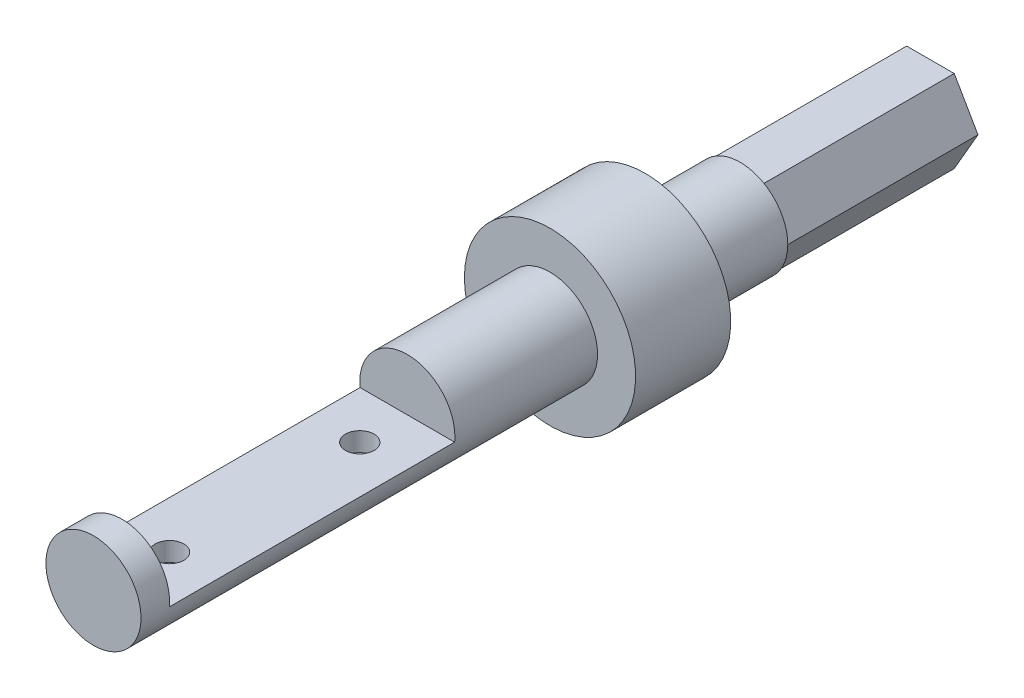
SolidWorks part; units mm, degrees
ref_plane "Front Plane" through (0, 0, 0) normal (0, 0, 1) x (1, 0, 0)
ref_plane "Top Plane" through (0, 0, 0) normal (0, 1, 0) x (1, 0, 0)
ref_plane "Right Plane" through (0, 0, 0) normal (1, 0, 0) x (0, 0, -1)
sketch "Sketch1" plane through (0, 0, 0) normal (0, 0, 1) x (1, 0, 0)
  circle A0 centre (0, 0) radius 5
extrude "Boss-Extrude1" add sketch "Sketch1" along normal blind 40
sketch "Sketch2" plane through (0, 0, 0) normal (0, 0, -1) x (-1, 0, 0)
  circle A0 centre (0, 0) radius 9
extrude "Boss-Extrude2" add sketch "Sketch2" along normal blind 10
sketch "Sketch3" plane through (0, 0, -10) normal (0, 0, -1) x (-1, 0, 0)
  circle A0 centre (0, 0) radius 5
extrude "Boss-Extrude3" add sketch "Sketch3" along normal blind 10
sketch "Sketch4" plane through (0, 0, -20) normal (0, 0, -1) x (-1, 0, 0)
  line L1 (-5, 0) -> (-2.5, -4.3301)
  line L2 (-2.5, -4.3301) -> (2.5, -4.3301)
  line L3 (2.5, -4.3301) -> (5, 0)
  line L4 (5, 0) -> (2.5, 4.3301)
  line L5 (2.5, 4.3301) -> (-2.5, 4.3301)
  line L6 (-2.5, 4.3301) -> (-5, 0)
  circle A0 centre (0, 0) radius 4.3301 construction
extrude "Boss-Extrude4" add sketch "Sketch4" along normal blind 20
sketch "Sketch5" plane through (0, 0, 0) normal (1, 0, 0) x (0, 0, -1)
  line L0 (0, 5) -> (-40, 5) construction
  line L1 (-45, 5) -> (-15, 5)
  line L2 (-45, 5) -> (-45, -0.5)
  line L3 (-45, -0.5) -> (-15, -0.5)
  line L4 (-15, 5) -> (-15, -0.5)
  dimension "D1" = 5.5
  dimension "D2" = 30
  dimension "D3" = 15
sketch "Sketch6" plane through (0, 0, 40) normal (0, 0, 1) x (1, 0, 0)
  circle A0 centre (0, 0) radius 5
extrude "Boss-Extrude5" add sketch "Sketch6" along normal blind 8
extrude "Cut-Extrude1" cut sketch "Sketch5" against normal through all both and the other way through all
sketch "Sketch8" plane through (0, -0.5, 0) normal (0, 1, 0) x (1, 0, 0)
  line L0 (0, -15) -> (0, -45) construction
  line L1 (-5, -15) -> (5, -15) construction
  line L2 (-4.9749, -45) -> (4.9749, -45) construction
  line L3 (0, -45) -> (0, -30) construction
  line L4 (0, -30) -> (4.9749, -30) construction
  line L5 (4.9749, -15) -> (4.9749, -45) construction
  circle A0 centre (0, -40) radius 1.5
  circle A1 centre (0, -20) radius 1.5
  point P12 (2.4875, -30)
  dimension "D1" = 3
  dimension "D2" = 10
extrude "Cut-Extrude2" cut sketch "Sketch8" against normal blind 2
